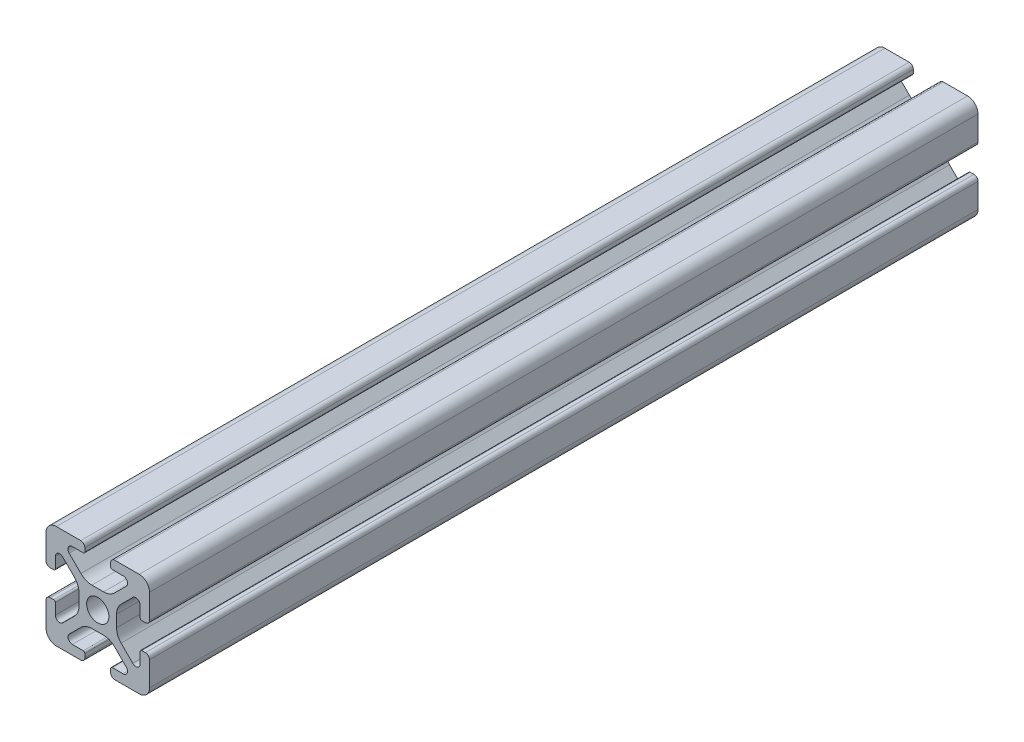
SolidWorks part; units mm, degrees
ref_plane "Front Plane" through (0, 0, 0) normal (0, 0, 1) x (1, 0, 0)
ref_plane "Top Plane" through (0, 0, 0) normal (0, 1, 0) x (1, 0, 0)
ref_plane "Right Plane" through (0, 0, 0) normal (1, 0, 0) x (0, 0, -1)
sketch "Sketch1" plane through (0, 0, 0) normal (0, 0, 1) x (1, 0, 0)
  line L2 (-9.9949, 7.9883) -> (-9.9949, 3.2893)
  line L3 (-7.9883, 9.9949) -> (-3.2893, 9.9949)
  line L4 (-2.5019, 9.2075) -> (-2.5019, 8.4963)
  line L5 (-2.8067, 8.1915) -> (-4.9149, 8.1915)
  line L6 (-5.5076, 6.7606) -> (-3.2528, 4.5058)
  line L7 (-6.7606, 5.5076) -> (-4.5058, 3.2528)
  line L8 (-8.1915, 4.9149) -> (-8.1915, 2.8067)
  line L9 (-8.4963, 2.5019) -> (-9.2075, 2.5019)
  line L11 (-1.1334, 3.6279) -> (1.1334, 3.6279)
  line L12 (-3.6279, 1.1334) -> (-3.6279, -1.1334)
  line L13 (8.4963, 2.5019) -> (9.2075, 2.5019)
  line L14 (8.1915, 4.9149) -> (8.1915, 2.8067)
  line L15 (9.9949, 7.9883) -> (9.9949, 3.2893)
  line L16 (7.9883, 9.9949) -> (3.2893, 9.9949)
  line L17 (2.5019, 9.2075) -> (2.5019, 8.4963)
  line L18 (2.8067, 8.1915) -> (4.9149, 8.1915)
  line L19 (3.6279, 1.1334) -> (3.6279, -1.1334)
  line L20 (5.5076, 6.7606) -> (3.2528, 4.5058)
  line L21 (6.7606, 5.5076) -> (4.5058, 3.2528)
  line L22 (-8.4963, -2.5019) -> (-9.2075, -2.5019)
  line L23 (-8.1915, -4.9149) -> (-8.1915, -2.8067)
  line L24 (-6.7606, -5.5076) -> (-4.5058, -3.2528)
  line L25 (-5.5076, -6.7606) -> (-3.2528, -4.5058)
  line L26 (-2.8067, -8.1915) -> (-4.9149, -8.1915)
  line L27 (-2.5019, -9.2075) -> (-2.5019, -8.4963)
  line L28 (-7.9883, -9.9949) -> (-3.2893, -9.9949)
  line L29 (-9.9949, -7.9883) -> (-9.9949, -3.2893)
  line L30 (9.9949, -7.9883) -> (9.9949, -3.2893)
  line L31 (7.9883, -9.9949) -> (3.2893, -9.9949)
  line L32 (2.5019, -9.2075) -> (2.5019, -8.4963)
  line L33 (2.8067, -8.1915) -> (4.9149, -8.1915)
  line L34 (5.5076, -6.7606) -> (3.2528, -4.5058)
  line L35 (6.7606, -5.5076) -> (4.5058, -3.2528)
  line L36 (8.1915, -4.9149) -> (8.1915, -2.8067)
  line L37 (8.4963, -2.5019) -> (9.2075, -2.5019)
  line L38 (-1.1334, -3.6279) -> (1.1334, -3.6279)
  circle A0 centre (0, 0) radius 2.1463
  arc A1 (-9.9949, 7.9883) -> (-7.9883, 9.9949) centre (-7.9883, 7.9883) cw
  arc A2 (-6.7606, 5.5076) -> (-8.1915, 4.9149) centre (-7.3533, 4.9149) ccw
  arc A3 (-4.9149, 8.1915) -> (-5.5076, 6.7606) centre (-4.9149, 7.3533) ccw
  arc A4 (-3.2893, 9.9949) -> (-2.5019, 9.2075) centre (-3.2893, 9.2075) cw
  arc A5 (-9.9949, 3.2893) -> (-9.2075, 2.5019) centre (-9.2075, 3.2893) ccw
  arc A6 (-8.1915, 2.8067) -> (-8.4963, 2.5019) centre (-8.4963, 2.8067) cw
  arc A7 (-2.5019, 8.4963) -> (-2.8067, 8.1915) centre (-2.8067, 8.4963) cw
  arc A8 (-1.1334, 3.6279) -> (-3.2528, 4.5058) centre (-1.1334, 6.6251) cw
  arc A9 (-3.6279, 1.1334) -> (-4.5058, 3.2528) centre (-6.6251, 1.1334) ccw
  arc A10 (8.1915, 2.8067) -> (8.4963, 2.5019) centre (8.4963, 2.8067) ccw
  arc A11 (9.9949, 3.2893) -> (9.2075, 2.5019) centre (9.2075, 3.2893) cw
  arc A12 (9.9949, 7.9883) -> (7.9883, 9.9949) centre (7.9883, 7.9883) ccw
  arc A13 (3.2893, 9.9949) -> (2.5019, 9.2075) centre (3.2893, 9.2075) ccw
  arc A14 (2.5019, 8.4963) -> (2.8067, 8.1915) centre (2.8067, 8.4963) ccw
  arc A15 (1.1334, 3.6279) -> (3.2528, 4.5058) centre (1.1334, 6.6251) ccw
  arc A16 (3.6279, 1.1334) -> (4.5058, 3.2528) centre (6.6251, 1.1334) cw
  arc A17 (6.7606, 5.5076) -> (8.1915, 4.9149) centre (7.3533, 4.9149) cw
  arc A18 (4.9149, 8.1915) -> (5.5076, 6.7606) centre (4.9149, 7.3533) cw
  arc A19 (-3.6279, -1.1334) -> (-4.5058, -3.2528) centre (-6.6251, -1.1334) cw
  arc A20 (-1.1334, -3.6279) -> (-3.2528, -4.5058) centre (-1.1334, -6.6251) ccw
  arc A21 (-2.5019, -8.4963) -> (-2.8067, -8.1915) centre (-2.8067, -8.4963) ccw
  arc A22 (-8.1915, -2.8067) -> (-8.4963, -2.5019) centre (-8.4963, -2.8067) ccw
  arc A23 (-9.9949, -3.2893) -> (-9.2075, -2.5019) centre (-9.2075, -3.2893) cw
  arc A24 (-3.2893, -9.9949) -> (-2.5019, -9.2075) centre (-3.2893, -9.2075) ccw
  arc A25 (-4.9149, -8.1915) -> (-5.5076, -6.7606) centre (-4.9149, -7.3533) cw
  arc A26 (-6.7606, -5.5076) -> (-8.1915, -4.9149) centre (-7.3533, -4.9149) cw
  arc A27 (-9.9949, -7.9883) -> (-7.9883, -9.9949) centre (-7.9883, -7.9883) ccw
  arc A28 (9.9949, -7.9883) -> (7.9883, -9.9949) centre (7.9883, -7.9883) cw
  arc A29 (6.7606, -5.5076) -> (8.1915, -4.9149) centre (7.3533, -4.9149) ccw
  arc A30 (4.9149, -8.1915) -> (5.5076, -6.7606) centre (4.9149, -7.3533) ccw
  arc A31 (3.2893, -9.9949) -> (2.5019, -9.2075) centre (3.2893, -9.2075) cw
  arc A32 (9.9949, -3.2893) -> (9.2075, -2.5019) centre (9.2075, -3.2893) ccw
  arc A33 (8.1915, -2.8067) -> (8.4963, -2.5019) centre (8.4963, -2.8067) cw
  arc A34 (2.5019, -8.4963) -> (2.8067, -8.1915) centre (2.8067, -8.4963) cw
  arc A35 (1.1334, -3.6279) -> (3.2528, -4.5058) centre (1.1334, -6.6251) cw
  arc A36 (3.6279, -1.1334) -> (4.5058, -3.2528) centre (6.6251, -1.1334) ccw
extrude "Boss-Extrude1" add sketch "Sketch1" along normal mid plane 160
